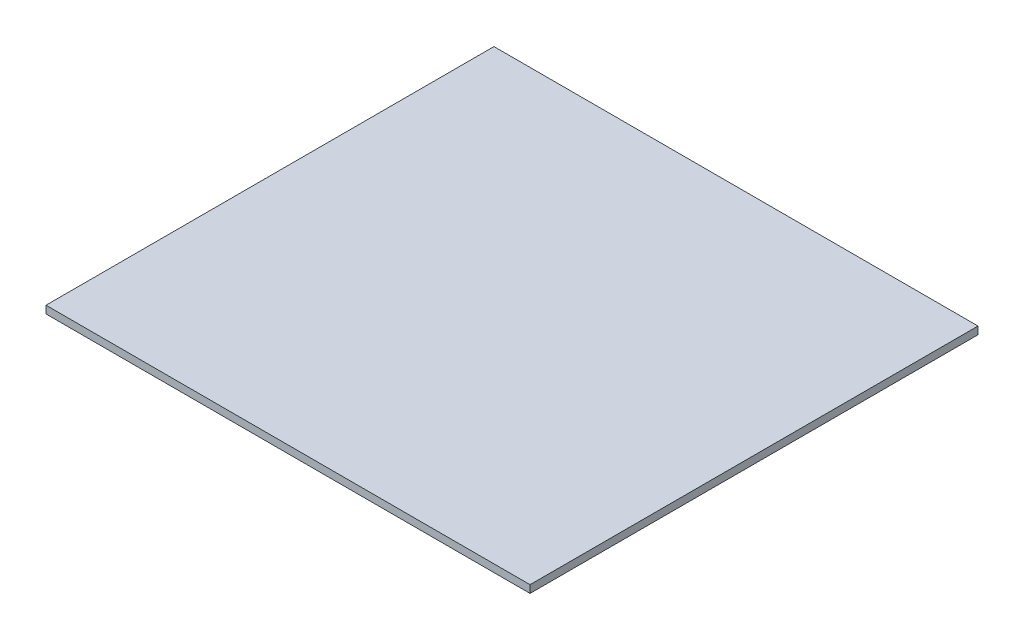
SolidWorks part; units mm, degrees
material "Pine"
ref_plane "Front Plane" through (0, 0, 0) normal (0, 0, 1) x (1, 0, 0)
ref_plane "Top Plane" through (0, 0, 0) normal (0, 1, 0) x (1, 0, 0)
ref_plane "Right Plane" through (0, 0, 0) normal (1, 0, 0) x (0, 0, -1)
sketch "Sketch1" plane through (0, 0, 0) normal (0, 1, 0) x (1, 0, 0)
  line L1 (-404.8125, -374.65) -> (404.8125, -374.65)
  line L2 (-404.8125, -374.65) -> (-404.8125, 374.65)
  line L3 (-404.8125, 374.65) -> (404.8125, 374.65)
  line L4 (404.8125, -374.65) -> (404.8125, 374.65)
  line L5 (-404.8125, -374.65) -> (404.8125, 374.65) construction
  line L6 (-404.8125, 374.65) -> (404.8125, -374.65) construction
  point P0 (0, 0)
  dimension "D1" = 749.3
  dimension "D2" = 809.625
extrude "Boss-Extrude1" add sketch "Sketch1" along normal mid plane 12.7
